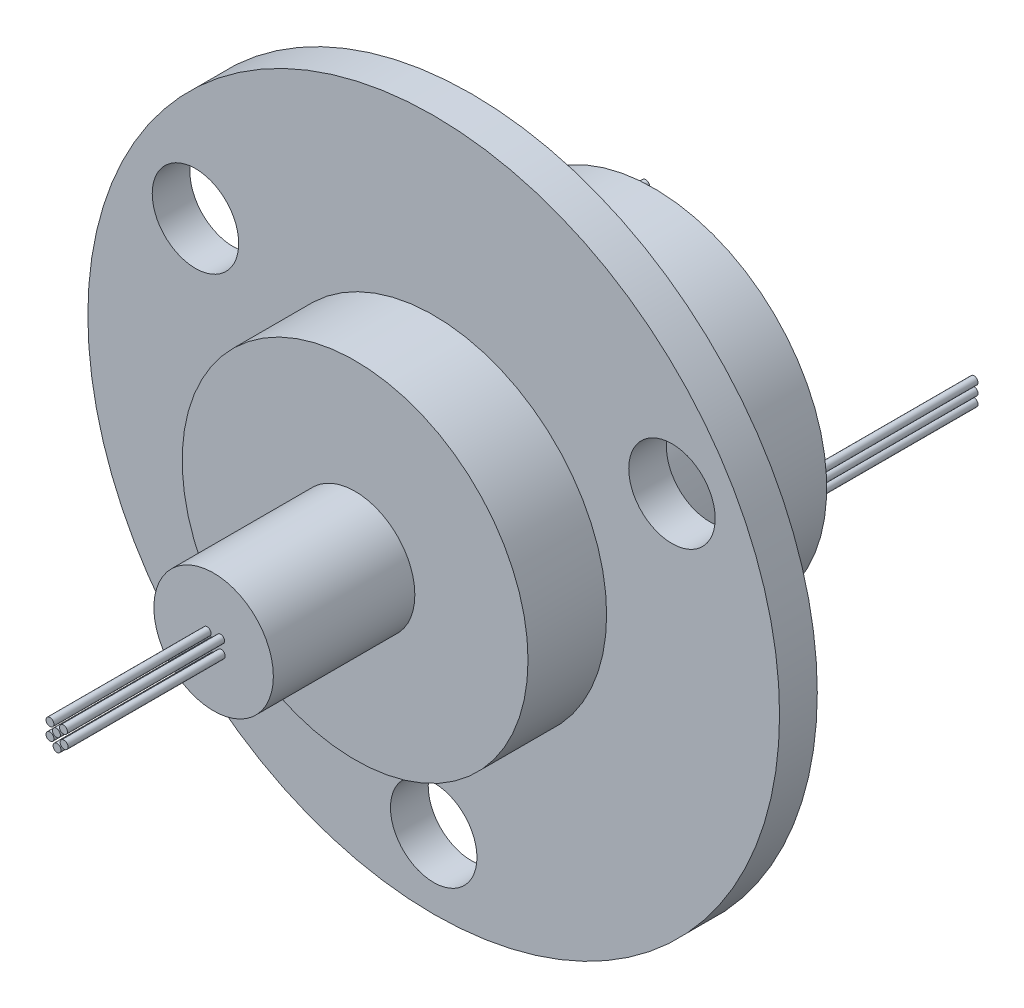
SolidWorks part; units mm, degrees
ref_plane "Front Plane" through (0, 0, 0) normal (0, 0, 1) x (1, 0, 0)
ref_plane "Top Plane" through (0, 0, 0) normal (0, 1, 0) x (1, 0, 0)
ref_plane "Right Plane" through (0, 0, 0) normal (1, 0, 0) x (0, 0, -1)
ref_plane "Plane1" through (0, 0, 0) normal (0, -1, 0) x (1, 0, 0)
sketch "Sketch1" plane through (0, 0, 0) normal (0, -1, 0) x (1, 0, 0)
  line L0 (22, 2.4) -> (0, 2.4)
  line L1 (0, 2.4) -> (0, 0)
  line L2 (0, 0) -> (22, 0)
  line L3 (22, 0) -> (22, 2.4)
  line L4 (0, 2.4) -> (0, 0) construction
revolve "Revolve1" add sketch "Sketch1" angle 360 about L4
sketch "Sketch2" plane through (0, 0, 2.4) normal (0, 0, 1) x (1, 0, 0)
  circle A0 centre (0, 0) radius 11
extrude "Boss-Extrude1" add sketch "Sketch2" along normal blind 5
sketch "Sketch3" plane through (0, 0, 7.4) normal (0, 0, 1) x (1, 0, 0)
  circle A0 centre (0, 0) radius 3.8
extrude "Boss-Extrude2" add sketch "Sketch3" along normal blind 9
sketch "Sketch4" plane through (0, 0, 16.4) normal (0, 0, 1) x (1, 0, 0)
  circle A0 centre (0, 0) radius 0.25
extrude "Boss-Extrude3" add sketch "Sketch4" along normal blind 10
sketch "Sketch5" plane through (0, 0, 0) normal (0, 0, -1) x (-1, 0, 0)
  circle A0 centre (0, 0) radius 11
extrude "Boss-Extrude4" add sketch "Sketch5" along normal blind 11.6
ref_plane "Plane2" through (0, -0.8163, 0) normal (0, -1, 0) x (1, 0, 0)
sketch "Sketch6" plane through (0, -0.8163, 0) normal (0, -1, 0) x (1, 0, 0)
  line L0 (0.2883, 26.4) -> (0.0383, 26.4)
  line L1 (0.0383, 26.4) -> (0.0383, 16.4)
  line L2 (0.0383, 16.4) -> (0.2883, 16.4)
  line L3 (0.2883, 16.4) -> (0.2883, 26.4)
  line L4 (0.0383, 26.4) -> (0.0383, 16.4) construction
revolve "Revolve2" add sketch "Sketch6" angle 360 about L4
ref_plane "Plane3" through (0, -0.4163, 0) normal (0, -1, 0) x (1, 0, 0)
sketch "Sketch7" plane through (0, -0.4163, 0) normal (0, -1, 0) x (1, 0, 0)
  line L0 (0.7383, 26.4) -> (0.4883, 26.4)
  line L1 (0.4883, 26.4) -> (0.4883, 16.4)
  line L2 (0.4883, 16.4) -> (0.7383, 16.4)
  line L3 (0.7383, 16.4) -> (0.7383, 26.4)
  line L4 (0.4883, 26.4) -> (0.4883, 16.4) construction
revolve "Revolve3" add sketch "Sketch7" angle 360 about L4
ref_plane "Plane4" through (0, 0.3837, 0) normal (0, -1, 0) x (1, 0, 0)
sketch "Sketch8" plane through (0, 0.3837, 0) normal (0, -1, 0) x (1, 0, 0)
  line L0 (-0.1617, 26.4) -> (-0.4117, 26.4)
  line L1 (-0.4117, 26.4) -> (-0.4117, 16.4)
  line L2 (-0.4117, 16.4) -> (-0.1617, 16.4)
  line L3 (-0.1617, 16.4) -> (-0.1617, 26.4)
  line L4 (-0.4117, 26.4) -> (-0.4117, 16.4) construction
revolve "Revolve4" add sketch "Sketch8" angle 360 about L4
ref_plane "Plane5" through (0, 0.4001, 0) normal (0, -1, 0) x (1, 0, 0)
sketch "Sketch9" plane through (0, 0.4001, 0) normal (0, -1, 0) x (1, 0, 0)
  line L0 (0.6974, 26.4) -> (0.4474, 26.4)
  line L1 (0.4474, 26.4) -> (0.4474, 16.4)
  line L2 (0.4474, 16.4) -> (0.6974, 16.4)
  line L3 (0.6974, 16.4) -> (0.6974, 26.4)
  line L4 (0.4474, 26.4) -> (0.4474, 16.4) construction
revolve "Revolve5" add sketch "Sketch9" angle 360 about L4
ref_plane "Plane6" through (0, -0.2224, 0) normal (0, 1, 0) x (1, 0, 0)
sketch "Sketch10" plane through (0, -0.2224, 0) normal (0, 1, 0) x (1, 0, 0)
  line L0 (-10.2674, 21.6) -> (-10.5174, 21.6)
  line L1 (-10.5174, 21.6) -> (-10.5174, 11.6)
  line L2 (-10.5174, 11.6) -> (-10.2674, 11.6)
  line L3 (-10.2674, 11.6) -> (-10.2674, 21.6)
  line L4 (-10.5174, 21.6) -> (-10.5174, 11.6) construction
revolve "Revolve6" add sketch "Sketch10" angle 360 about L4
ref_plane "Plane7" through (0, 0.3776, 0) normal (0, 1, 0) x (1, 0, 0)
sketch "Sketch11" plane through (0, 0.3776, 0) normal (0, 1, 0) x (1, 0, 0)
  line L0 (-10.2674, 21.6) -> (-10.5174, 21.6)
  line L1 (-10.5174, 21.6) -> (-10.5174, 11.6)
  line L2 (-10.5174, 11.6) -> (-10.2674, 11.6)
  line L3 (-10.2674, 11.6) -> (-10.2674, 21.6)
  line L4 (-10.5174, 21.6) -> (-10.5174, 11.6) construction
revolve "Revolve7" add sketch "Sketch11" angle 360 about L4
ref_plane "Plane8" through (0, 0.6, 0) normal (0, 1, 0) x (1, 0, 0)
sketch "Sketch12" plane through (0, 0.6, 0) normal (0, 1, 0) x (1, 0, 0)
  line L0 (10.6217, 21.6) -> (10.3717, 21.6)
  line L1 (10.3717, 21.6) -> (10.3717, 11.6)
  line L2 (10.3717, 11.6) -> (10.6217, 11.6)
  line L3 (10.6217, 11.6) -> (10.6217, 21.6)
  line L4 (10.3717, 21.6) -> (10.3717, 11.6) construction
revolve "Revolve8" add sketch "Sketch12" angle 360 about L4
sketch "Sketch13" plane through (0, 0, 0) normal (0, 1, 0) x (1, 0, 0)
  line L0 (10.6217, 21.6) -> (10.3717, 21.6)
  line L1 (10.3717, 21.6) -> (10.3717, 11.6)
  line L2 (10.3717, 11.6) -> (10.6217, 11.6)
  line L3 (10.6217, 11.6) -> (10.6217, 21.6)
  line L4 (10.3717, 21.6) -> (10.3717, 11.6) construction
revolve "Revolve9" add sketch "Sketch13" angle 360 about L4
ref_plane "Plane9" through (0, -0.6, 0) normal (0, 1, 0) x (1, 0, 0)
sketch "Sketch14" plane through (0, -0.6, 0) normal (0, 1, 0) x (1, 0, 0)
  line L0 (10.6217, 21.6) -> (10.3717, 21.6)
  line L1 (10.3717, 21.6) -> (10.3717, 11.6)
  line L2 (10.3717, 11.6) -> (10.6217, 11.6)
  line L3 (10.6217, 11.6) -> (10.6217, 21.6)
  line L4 (10.3717, 21.6) -> (10.3717, 11.6) construction
revolve "Revolve10" add sketch "Sketch14" angle 360 about L4
ref_plane "Plane10" through (0, 0.9686, 0) normal (0, 1, 0) x (1, 0, 0)
sketch "Sketch15" plane through (0, 0.9686, 0) normal (0, 1, 0) x (1, 0, 0)
  line L0 (-10.2674, 21.6) -> (-10.5174, 21.6)
  line L1 (-10.5174, 21.6) -> (-10.5174, 11.6)
  line L2 (-10.5174, 11.6) -> (-10.2674, 11.6)
  line L3 (-10.2674, 11.6) -> (-10.2674, 21.6)
  line L4 (-10.5174, 21.6) -> (-10.5174, 11.6) construction
revolve "Revolve11" add sketch "Sketch15" angle 360 about L4
sketch "Sketch16" plane through (0, -0.4163, 0) normal (0, -1, 0) x (1, 0, 0)
  line L0 (-0.1617, 26.4) -> (-0.4117, 26.4)
  line L1 (-0.4117, 26.4) -> (-0.4117, 16.4)
  line L2 (-0.4117, 16.4) -> (-0.1617, 16.4)
  line L3 (-0.1617, 16.4) -> (-0.1617, 26.4)
  line L4 (-0.4117, 26.4) -> (-0.4117, 16.4) construction
revolve "Revolve12" add sketch "Sketch16" angle 360 about L4
hole_wizard "Ø5.5 (5.5) Diameter Hole1" positions "Sketch18" profile "Sketch17" hole size "Ø5.5" standard "ANSI Metric"
sketch "Sketch18" plane through (0, 0, 0) normal (0, 0, -1) x (-1, 0, 0)
  point P0 (-15.1554, 8.75)
  point P1 (15.1554, 8.75)
  point P2 (0, -17.5)
sketch "Sketch17" plane through (15.1554, 8.75, 0) normal (1, 0, 0) x (0, 1, 0)
  line L0 (0, 0) -> (0, 26.4)
  line L1 (0, 26.4) -> (2.75, 26.4)
  line L2 (2.75, 26.4) -> (2.75, 0)
  line L5 (2.75, 0) -> (0, 0)
  line L11 (0, -6.35) -> (0, 107.95) construction
  dimension "Thru Hole Dia." = 5.5
  dimension "Thru Hole Depth" = 26.4
